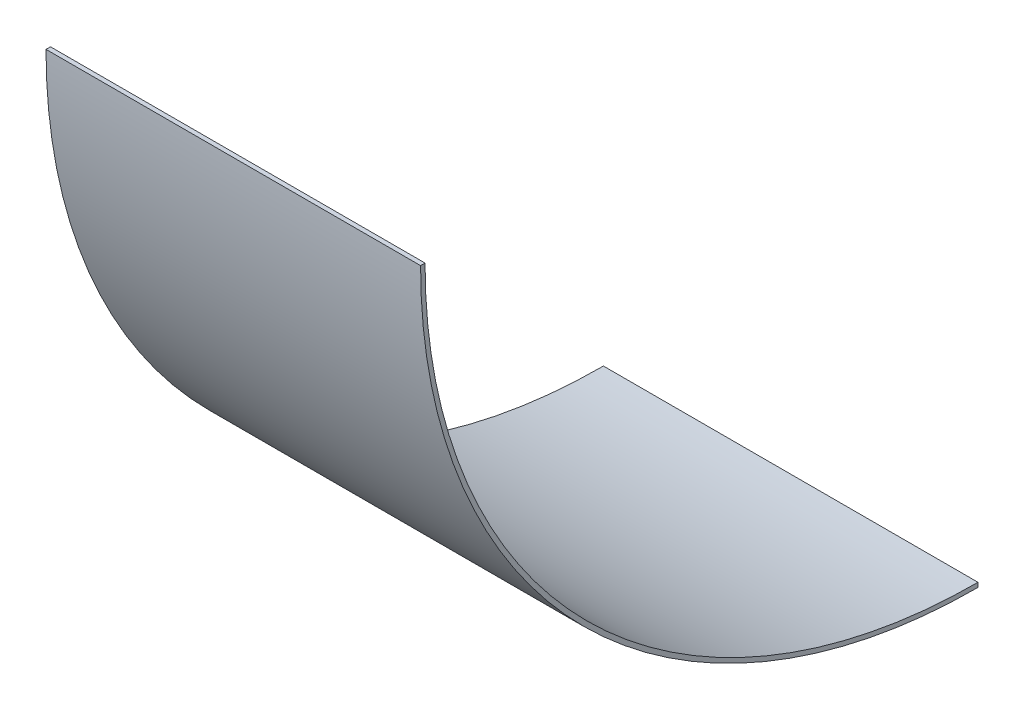
SolidWorks part; units mm, degrees
ref_plane "Front Plane" through (0, 0, 0) normal (0, 0, 1) x (1, 0, 0)
ref_plane "Top Plane" through (0, 0, 0) normal (0, 1, 0) x (1, 0, 0)
ref_plane "Right Plane" through (0, 0, 0) normal (1, 0, 0) x (0, 0, -1)
sketch "Sketch1" plane through (0, 0, 0) normal (1, 0, 0) x (0, 0, -1)
  arc A0 (-196.85, 0) -> (0, -196.85) centre (0, 0) ccw
  dimension "D1" = 196.85
extrude "Extrude-Thin1" add sketch "Sketch1" along normal blind 133.35 thin
